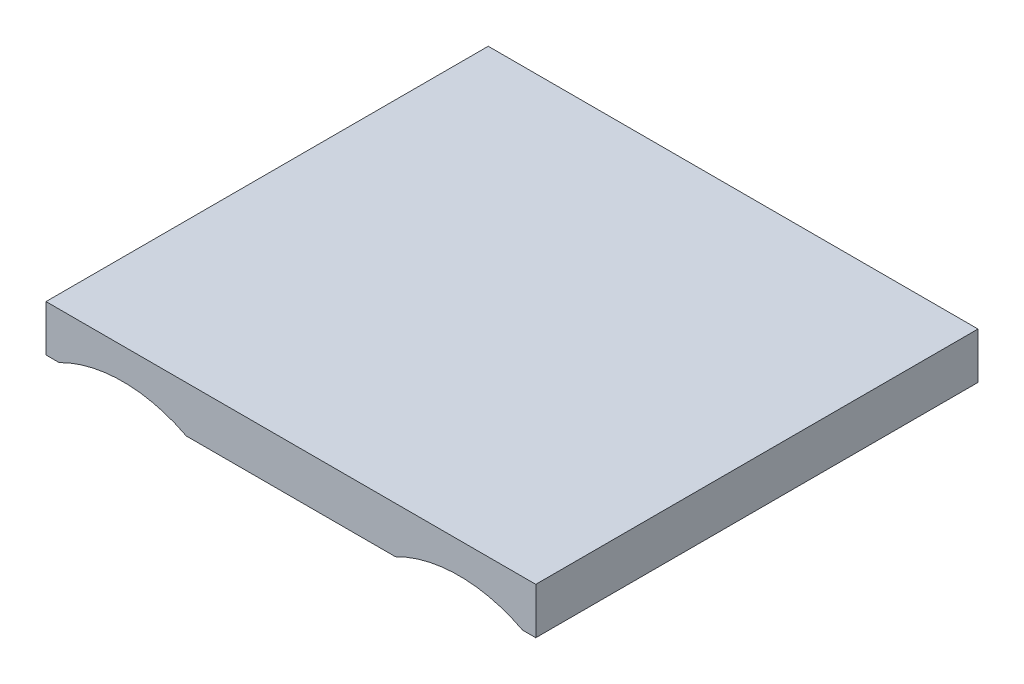
SolidWorks part; units mm, degrees
material "Melamine resin"
ref_plane "Front Plane" through (0, 0, 0) normal (0, 0, 1) x (1, 0, 0)
ref_plane "Top Plane" through (0, 0, 0) normal (0, 1, 0) x (1, 0, 0)
ref_plane "Right Plane" through (0, 0, 0) normal (1, 0, 0) x (0, 0, -1)
sketch "Sketch1" plane through (0, 0, 0) normal (0, 0, 1) x (1, 0, 0)
  line L0 (0, 0) -> (0, -1.5) construction
  line L1 (-15.875, -1.5) -> (-15.0231, -1.5)
  line L2 (-15.875, -1.5) -> (-15.875, 1.5)
  line L3 (-15.875, 1.5) -> (15.875, 1.5)
  line L4 (15.875, -1.5) -> (15.875, 1.5)
  line L5 (-15.875, -1.5) -> (15.875, 1.5) construction
  line L6 (-15.875, 1.5) -> (15.875, -1.5) construction
  line L7 (-6.7769, -1.5) -> (6.7769, -1.5)
  line L8 (15.0231, -1.5) -> (15.875, -1.5)
  arc A0 (-6.7769, -1.5) -> (-15.0231, -1.5) centre (-10.9, -9.5) ccw
  arc A1 (6.7769, -1.5) -> (15.0231, -1.5) centre (10.9, -9.5) cw
  point P0 (0, 0)
  point P6 (0, -1.5)
  point P10 (-6.6596, -1.5)
  point P11 (-5.7666, -4.9086)
  point P14 (-6.1053, -6.5)
  dimension "D1" = 3
  dimension "D2" = 18
  dimension "D3" = 31.75
  dimension "D4" = 8
  dimension "D5" = 21.8
extrude "Boss-Extrude1" add sketch "Sketch1" along normal blind 28.668 contours L3 L4 L8 A1 L7 A0 L1 L2
sketch "Sketch2" plane through (0, 0, 28.668) normal (0, 0, 1) x (1, 0, 0)
  line L0 (15.875, -1.5) -> (15.875, 1.5) construction
  line L1 (-15.875, -1.5) -> (15.875, -1.5)
  line L2 (-15.875, -1.5) -> (-15.875, -0.5)
  line L3 (-15.875, -0.5) -> (15.875, -0.5)
  line L4 (15.875, -1.5) -> (15.875, -0.5)
  dimension "D1" = 1
ref_plane "Plane1" through (0, 0, 14.334) normal (0, 0, 1) x (1, 0, 0)
